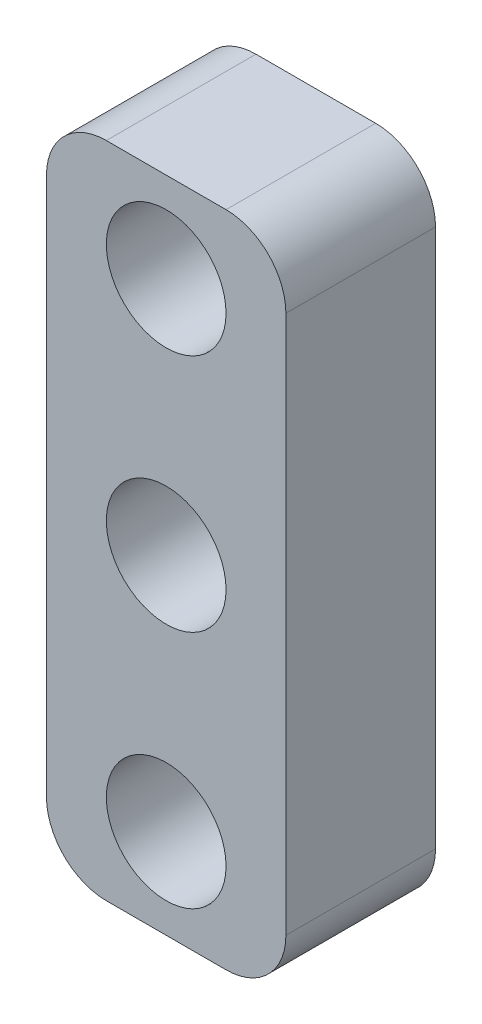
SolidWorks part; units mm, degrees
ref_plane "Front Plane" through (0, 0, 0) normal (0, 0, 1) x (1, 0, 0)
ref_plane "Top Plane" through (0, 0, 0) normal (0, 1, 0) x (1, 0, 0)
ref_plane "Right Plane" through (0, 0, 0) normal (1, 0, 0) x (0, 0, -1)
sketch "Sketch1" plane through (0, 0, 0) normal (0, 0, 1) x (1, 0, 0)
  line L0 (0, -9) -> (0, 9)
  line L1 (8, -9) -> (8, 9)
  line L2 (2, 11) -> (6, 11)
  line L3 (2, -11) -> (6, -11)
  line L4 (8, -14.5) -> (8, 14.5) construction
  line L5 (0, -14.5) -> (0, 14.5) construction
  arc A0 (8, 9) -> (6, 11) centre (6, 9) ccw
  arc A1 (0, 9) -> (2, 11) centre (2, 9) cw
  arc A2 (0, -9) -> (2, -11) centre (2, -9) ccw
  arc A3 (8, -9) -> (6, -11) centre (6, -9) cw
  point P4 (0, 0)
  point P13 (0, 11)
  dimension "D3" = 2
  dimension "D1" = 22
  dimension "D2" = 8
extrude "Boss-Extrude1" add sketch "Sketch1" along normal blind 5
sketch "Sketch3" plane through (0, 0, 5) normal (0, 0, 1) x (1, 0, 0)
  line L0 (0, 0) -> (10.5795, 0) construction
  line L1 (4, 11) -> (4, -16.6132) construction
  line L2 (6, 11) -> (2, 11) construction
  circle A0 centre (4, 0) radius 2
  circle A1 centre (4, 8) radius 2
  circle A2 centre (4, -8) radius 2
  dimension "D1" = 4
  dimension "D2" = 4
  dimension "D3" = 4
  dimension "D4" = 8
  dimension "D5" = 8
extrude "Cut-Extrude2" cut sketch "Sketch3" against normal through all
